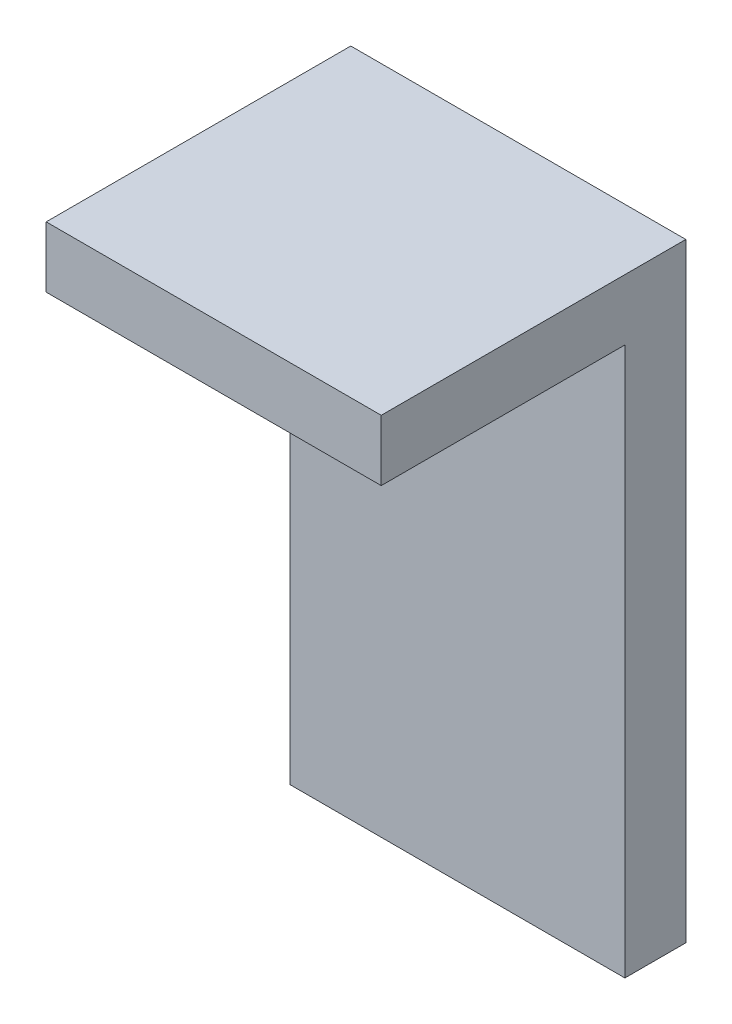
SolidWorks part; units mm, degrees
ref_plane "Front Plane" through (0, 0, 0) normal (0, 0, 1) x (1, 0, 0)
ref_plane "Top Plane" through (0, 0, 0) normal (0, 1, 0) x (1, 0, 0)
ref_plane "Right Plane" through (0, 0, 0) normal (1, 0, 0) x (0, 0, -1)
sketch "Sketch1" plane through (0, 0, 0) normal (0, 0, 1) x (1, 0, 0)
  line L1 (0, 0) -> (55, 0)
  line L2 (0, 0) -> (0, 100)
  line L3 (0, 100) -> (55, 100)
  line L4 (55, 0) -> (55, 100)
  dimension "D1" = 100
  dimension "D2" = 55
extrude "Boss-Extrude1" add sketch "Sketch1" along normal blind 10
sketch "Sketch2" plane through (0, 0, 10) normal (0, 0, 1) x (1, 0, 0)
  line L0 (55, 0) -> (55, 100) construction
  line L1 (0, 100) -> (55, 100)
  line L2 (0, 100) -> (0, 90)
  line L3 (0, 90) -> (55, 90)
  line L4 (55, 100) -> (55, 90)
  dimension "D1" = 10
extrude "Boss-Extrude2" add sketch "Sketch2" along normal blind 40
